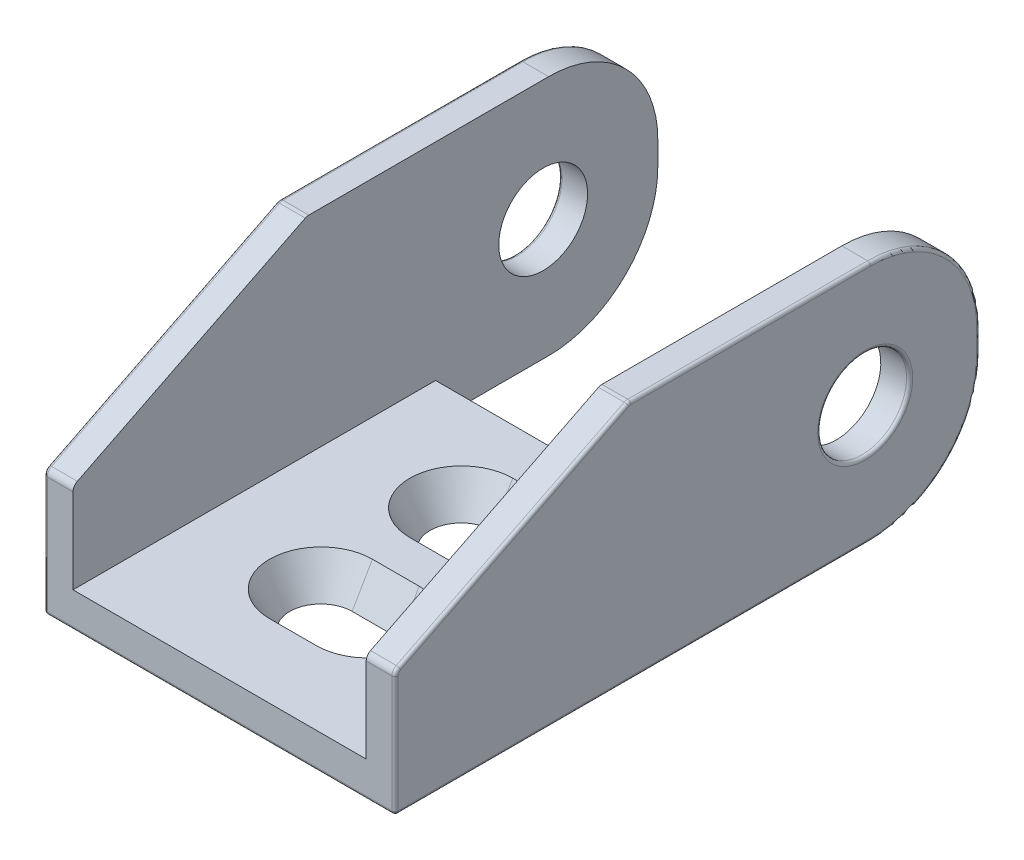
SolidWorks part; units mm, degrees
material "ABS"
ref_plane "Front Plane" through (0, 0, 0) normal (0, 0, 1) x (1, 0, 0)
ref_plane "Top Plane" through (0, 0, 0) normal (0, 1, 0) x (1, 0, 0)
ref_plane "Right Plane" through (0, 0, 0) normal (1, 0, 0) x (0, 0, -1)
sketch "Sketch1" plane through (0, 0, 0) normal (1, 0, 0) x (0, 0, -1)
  line L0 (0, 0) -> (0, 2.85) construction
  line L1 (0, 0) -> (0, -2.85) construction
  line L2 (0, 2.85) -> (0, 7.75) construction
  line L3 (0, -2.85) -> (0, -7.75) construction
  line L4 (0, 0) -> (2.85, 0) construction
  line L5 (2.85, 0) -> (7.35, 0) construction
  line L6 (7.35, 7.75) -> (7.35, -7.75)
  line L7 (7.35, 7.75) -> (-15.15, 7.75)
  line L8 (7.35, -7.75) -> (-30.15, -7.75)
  line L9 (-30.15, -7.75) -> (-30.15, 0.25)
  line L10 (-30.15, 0.25) -> (-15.15, 7.75)
  circle A0 centre (0, 0) radius 2.85
  dimension "D3" = 5.7
  dimension "D1" = 4.5
  dimension "D2" = 15.5
  dimension "D4" = 37.5
  dimension "D5" = 8
  dimension "D6" = 22.5
extrude "Boss-Extrude1" add sketch "Sketch1" along normal mid plane 22.5
sketch "Sketch2" plane through (0, 0, 0) normal (0, 0, 1) x (1, 0, 0)
  line L0 (0, 0) -> (0, 7.75) construction
  line L1 (11.25, 7.75) -> (-11.25, 7.75) construction
  line L2 (0, 0) -> (0, -5.5) construction
  line L4 (-9.4, 7.75) -> (9.4, 7.75)
  line L5 (-9.4, 7.75) -> (-9.4, -5.5)
  line L6 (-9.4, -5.5) -> (9.4, -5.5)
  line L7 (9.4, 7.75) -> (9.4, -5.5)
  line L10 (-11.25, 7.75) -> (-11.25, 0.25) construction
  line L11 (11.25, 7.75) -> (11.25, 0.25) construction
  line L12 (0, -5.5) -> (0, -7.75) construction
  line L13 (11.25, -7.75) -> (-11.25, -7.75) construction
  dimension "D1" = 18.8
  dimension "D2" = 1.85
  dimension "D3" = 1.85
  dimension "D4" = 2.25
extrude "Cut-Extrude1" cut sketch "Sketch2" against normal through all both and the other way through all
sketch "Sketch3" plane through (0, -5.5, 0) normal (0, 1, 0) x (1, 0, 0)
  line L0 (9.4, 7.35) -> (9.4, -15.15) construction
  line L1 (-9.4, 7.35) -> (9.4, 7.35)
  line L2 (-9.4, 7.35) -> (-9.4, -4.65)
  line L3 (-9.4, -4.65) -> (9.4, -4.65)
  line L4 (9.4, 7.35) -> (9.4, -4.65)
  line L5 (0, 0) -> (0, -4.65) construction
  line L6 (0, -4.65) -> (0, -30.15) construction
  line L7 (-9.4, -30.15) -> (9.4, -30.15) construction
  line L8 (0, 0) -> (0, 7.35) construction
  dimension "D1" = 25.5
extrude "Cut-Extrude2" cut sketch "Sketch3" against normal up to surface (2.25 mm away) up to face at (0, -7.75, 11.4)
fillet "Fillet1" radius 7 4 edges at (10.325, 7.75, -7.35) (10.325, -7.75, -7.35) (-10.325, 7.75, -7.35) (-10.325, -7.75, -7.35)
sketch "Sketch4" plane through (0, -7.75, 0) normal (0, -1, 0) x (1, 0, 0)
  line L0 (0, 0) -> (0, 4.65) construction
  line L1 (9.4, 4.65) -> (-9.4, 4.65) construction
  line L2 (0, 4.65) -> (0, 11.15) construction
  line L3 (-1.5, 22.15) -> (1.5, 22.15) construction
  line L4 (0, 24.15) -> (0, 30.15) construction
  line L5 (11.25, 30.15) -> (-11.25, 30.15) construction
  line L6 (0, 20.15) -> (0, 15.15) construction
  line L7 (-1.5, 24.15) -> (1.5, 24.15)
  line L8 (-1.5, 20.15) -> (1.5, 20.15)
  line L11 (-1.5, 13.15) -> (1.5, 13.15) construction
  line L16 (-1.5, 15.15) -> (1.5, 15.15)
  line L17 (-1.5, 11.15) -> (1.5, 11.15)
  line L18 (0, 24.15) -> (0, 20.15) construction
  line L19 (0, 15.15) -> (0, 11.15) construction
  line L20 (1.5, 22.15) -> (3.5, 22.15) construction
  line L21 (-1.5, 22.15) -> (-3.5, 22.15) construction
  arc A6 (-1.5, 24.15) -> (-1.5, 20.15) centre (-1.5, 22.15) ccw
  arc A7 (1.5, 20.15) -> (1.5, 24.15) centre (1.5, 22.15) ccw
  arc A8 (-1.5, 15.15) -> (-1.5, 11.15) centre (-1.5, 13.15) ccw
  arc A9 (1.5, 11.15) -> (1.5, 15.15) centre (1.5, 13.15) ccw
  point P14 (0, 22.15)
  point P21 (0, 13.15)
  dimension "D1" = 4
  dimension "D2" = 5
  dimension "D3" = 6
  dimension "D4" = 7
extrude "Cut-Extrude3" cut sketch "Sketch4" against normal up to surface (2.25 mm away) draft 30
sketch "Sketch5" plane through (9.4, 0, 0) normal (-1, 0, 0) x (0, 0, 1)
  line L0 (4.65, -7.75) -> (4.65, -5.5)
  line L1 (4.65, -5.5) -> (6.9, -5.5)
  line L2 (4.65, -5.5) -> (30.15, -5.5) construction
  line L3 (6.9, -5.5) -> (4.65, -7.75)
extrude "Cut-Extrude4" cut sketch "Sketch5" along normal up to surface (18.8 mm away) up to face at (-9.4, -2.85, 0)
sketch "Sketch6" plane through (0, -7.75, 0) normal (0, -1, 0) x (1, 0, 0)
  line L0 (0, 0) -> (0, 11.15) construction
  line L1 (-1.5, 11.15) -> (1.5, 11.15) construction
  line L2 (0, 11.15) -> (0, 15.15) construction
  line L3 (1.5, 15.15) -> (-1.5, 15.15) construction
  line L4 (0, 15.15) -> (0, 20.15) construction
  line L5 (-1.5, 20.15) -> (1.5, 20.15) construction
  line L6 (0, 20.15) -> (0, 24.15) construction
  line L7 (1.5, 24.15) -> (-1.5, 24.15) construction
  line L8 (0, 24.15) -> (0, 30.15) construction
  line L9 (11.25, 30.15) -> (-11.25, 30.15) construction
  line L11 (-6, 19.65) -> (6, 19.65)
  line L12 (-6, 19.65) -> (-6, 15.65)
  line L13 (-6, 15.65) -> (6, 15.65)
  line L14 (6, 19.65) -> (6, 15.65)
  line L15 (-6, 19.65) -> (6, 15.65) construction
  line L16 (-6, 15.65) -> (6, 19.65) construction
  point P8 (0, 17.65)
  dimension "D1" = 4
  dimension "D2" = 12
extrude "Cut-Extrude5" cut sketch "Sketch6" against normal blind 0.8
sketch "Sketch7" plane through (0, -6.95, 0) normal (0, -1, 0) x (1, 0, 0)
  line L0 (5.2624, 18.8988) -> (-6, 18.8988) construction
  line L2 (-6, 19.65) -> (-6, 15.65) construction
  line L3 (5.2624, 18.8988) -> (6, 18.8988) construction
  line L4 (6, 15.65) -> (6, 19.65) construction
  text T0 "10X15" font "Century Gothic" height 2.5
extrude "Boss-Extrude2" add sketch "Sketch7" along normal blind 0.15
fillet "Fillet2" radius 0.5 4 edges at (10.325, 0.25, 30.15) (-10.325, 0.25, 30.15) (10.325, 7.75, 15.15) (-10.325, 7.75, 15.15)
fillet "Fillet3" radius 0.2 21 edges at (-11.25, -7.75, 14.9) (-11.25, -5.6997, -5.2997) (-11.25, 0, -7.35) (-11.25, 5.6997, -5.2997) (-11.25, -3.9045, 30.15) (-11.25, 0.2038, 30.0753) (-11.25, 4.0427, 22.5646) (-11.25, 7.7366, 15.1468) (11.25, -7.75, 14.9) (11.25, -5.6997, -5.2997) (11.25, 0, -7.35) (11.25, 5.6997, -5.2997) (11.25, -3.9045, 30.15) (11.25, 0.2038, 30.0753) (11.25, 4.0427, 22.5646) (11.25, 7.7366, 15.1468) (-11.25, 7.75, 7.341) (11.25, 7.75, 7.341) (0, -7.75, 30.15) (-11.25, 0, -2.85) (11.25, 0, -2.85)
